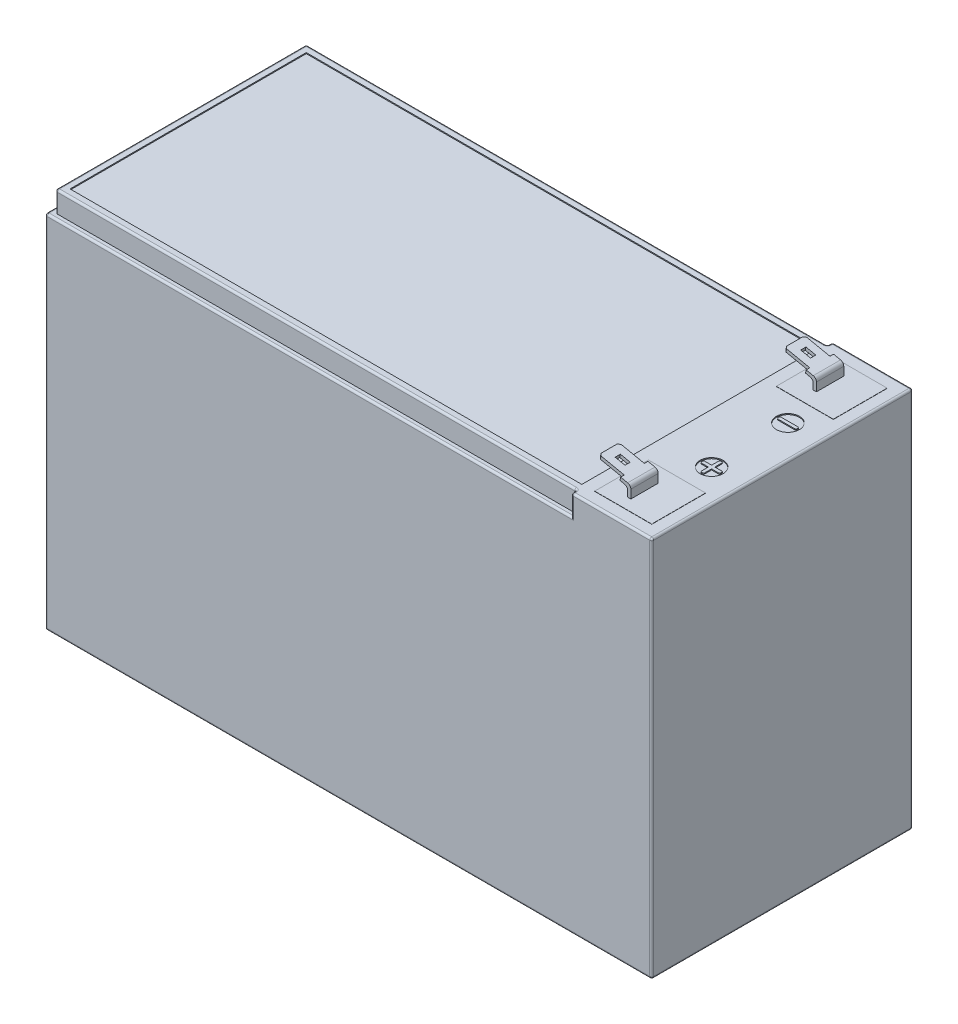
SolidWorks part; units mm, degrees
ref_plane "Front Plane" through (0, 0, 0) normal (0, 0, 1) x (1, 0, 0)
ref_plane "Top Plane" through (0, 0, 0) normal (0, 1, 0) x (1, 0, 0)
ref_plane "Right Plane" through (0, 0, 0) normal (1, 0, 0) x (0, 0, -1)
sketch "Sketch1" plane through (0, 0, 0) normal (0, 1, 0) x (1, 0, 0)
  line L1 (-75.0564, 43.5611) -> (75.9436, 43.5611)
  line L2 (-75.0564, 43.5611) -> (-75.0564, -21.4389)
  line L3 (-75.0564, -21.4389) -> (75.9436, -21.4389)
  line L4 (75.9436, 43.5611) -> (75.9436, -21.4389)
  dimension "D1" = 151
  dimension "D2" = 65
extrude "Boss-Extrude1" add sketch "Sketch1" along normal blind 95
ref_plane "Plane1" through (0, 0, 15.4389) normal (0, 0, 1) x (1, 0, 0)
sketch "Sketch2" plane through (0, 0, 15.4389) normal (0, 0, 1) x (1, 0, 0)
  line L0 (63.9436, 95) -> (63.9436, 97.3257)
  line L1 (-75.0564, 95) -> (75.9436, 95) construction
  line L2 (63.9436, 97.3257) -> (55.7698, 99.03)
  line L3 (55.7698, 99.03) -> (55.9331, 99.8131)
  line L4 (55.9331, 99.8131) -> (64.7436, 97.9761)
  line L5 (64.7436, 97.9761) -> (64.7436, 95)
  line L6 (64.7436, 95) -> (63.9436, 95)
  line L7 (75.9436, 95) -> (75.9436, 0) construction
  dimension "D1" = 12
  dimension "D2" = 9
  dimension "D3" = 0.8
  dimension "D4" = 0.8
extrude "Boss-Extrude2" add sketch "Sketch2" against normal blind 6.8
ref_plane "Plane2" through (0, 0, -11.0611) normal (0, 0, 1) x (1, 0, 0)
sketch "Sketch4" plane through (22.274, 106.8309, 0) normal (0.2041, 0.9789, 0) x (0.9789, -0.2041, 0)
  line L0 (40.7829, -8.6389) -> (40.7829, -9.5389)
  line L1 (43.3829, -8.6389) -> (34.3829, -8.6389) construction
  line L2 (40.7829, -9.5389) -> (34.3829, -9.5389)
  line L3 (34.3829, -8.6389) -> (34.3829, -15.4389) construction
  line L4 (34.3829, -9.5389) -> (34.3829, -8.6389)
  line L5 (34.3829, -8.6389) -> (40.7829, -8.6389)
  line L6 (40.7829, -14.5389) -> (40.7829, -15.4389)
  line L7 (-52.25, -15.4389) -> (52.25, -15.4389) construction
  line L8 (40.7829, -14.5389) -> (34.3829, -14.5389)
  line L9 (34.3829, -14.5389) -> (34.3829, -15.4389)
  line L10 (34.3829, -15.4389) -> (40.7829, -15.4389)
  line L12 (36.5829, -11.3889) -> (39.0829, -11.3889)
  line L13 (36.5829, -11.3889) -> (36.5829, -12.6889)
  line L14 (36.5829, -12.6889) -> (39.0829, -12.6889)
  line L15 (39.0829, -11.3889) -> (39.0829, -12.6889)
  dimension "D1" = 0.9
  dimension "D2" = 0.9
  dimension "D3" = 6.4
  dimension "D4" = 2.2
  dimension "D5" = 2.5
  dimension "D6" = 1.3
  dimension "D7" = 1.85
  dimension "D8" = 1.85
extrude "Cut-Extrude1" cut sketch "Sketch4" against normal up to next (0.8 mm away)
chamfer "Chamfer1" distance 0.5 angle 45 2 edges at (55.8514, 99.4215, 9.5389) (55.8514, 99.4215, 14.5389)
fillet "Fillet1" radius 1 2 edges at (63.9436, 97.3257, 12.0389) (64.7436, 97.9761, 12.0389)
mirror "Mirror1" about plane through (0, 0, -11.0611) normal (0, 0, 1) of "Fillet1", "Chamfer1", "Cut-Extrude1", "Boss-Extrude2"
sketch "Sketch5" plane through (0, 95, 0) normal (0, 1, 0) x (1, 0, 0)
  line L0 (55.9436, -21.4389) -> (55.9436, -20.1389)
  line L1 (-75.0564, -21.4389) -> (75.9436, -21.4389) construction
  line L2 (55.9436, -20.1389) -> (-73.7564, -20.1389)
  line L3 (-73.7564, -20.1389) -> (-73.7564, 42.2611)
  line L4 (-73.7564, 42.2611) -> (55.9436, 42.2611)
  line L5 (55.9436, 42.2611) -> (55.9436, 43.5611)
  line L6 (75.9436, 43.5611) -> (-75.0564, 43.5611) construction
  line L7 (55.9436, 43.5611) -> (-75.0564, 43.5611)
  line L8 (-75.0564, 43.5611) -> (-75.0564, -21.4389)
  line L9 (-75.0564, -21.4389) -> (55.9436, -21.4389)
  line L10 (75.9436, -21.4389) -> (75.9436, 43.5611) construction
  dimension "D1" = 1.3
  dimension "D2" = 1.3
  dimension "D3" = 1.3
  dimension "D4" = 20
  dimension "D5" = 20
extrude "Cut-Extrude2" cut sketch "Sketch5" against normal blind 5.2
fillet "Fillet2" radius 0.5 25 edges at (0.4436, 0, -43.5611) (-75.0564, 44.9, -43.5611) (-75.0564, 0, -11.0611) (-75.0564, 44.9, 21.4389) (75.9436, 0, -11.0611) (0.4436, 0, 21.4389) (75.9436, 47.5, -43.5611) (65.9436, 95, -43.5611) (55.9436, 92.4, -43.5611) (55.9436, 92.4, -42.2611) (55.9436, 95, -42.9111) (-9.5564, 89.8, -43.5611) (-8.9064, 95, -42.2611) (-73.7564, 92.4, -42.2611) (-73.7564, 92.4, 20.1389) (-75.0564, 89.8, -11.0611) (55.9436, 92.4, 20.1389) (-9.5564, 89.8, 21.4389) (55.9436, 92.4, 21.4389) (75.9436, 47.5, 21.4389) (75.9436, 95, -11.0611) (65.9436, 95, 21.4389) (55.9436, 95, 20.7889) (-8.9064, 95, 20.1389) (-73.7564, 95, -11.0611)
sketch "Sketch6" plane through (0, 95, 0) normal (0, 1, 0) x (1, 0, 0)
  line L0 (-73.7564, -19.6389) -> (-73.7564, 41.7611) construction
  line L1 (-71.9564, 40.4611) -> (55.4436, 40.4611)
  line L2 (-71.9564, 40.4611) -> (-71.9564, -18.3389)
  line L3 (-71.9564, -18.3389) -> (55.4436, -18.3389)
  line L4 (55.4436, 40.4611) -> (55.4436, -18.3389)
  line L5 (-73.2564, 42.2611) -> (55.4436, 42.2611) construction
  line L6 (55.4436, -20.1389) -> (-73.2564, -20.1389) construction
  line L7 (75.9436, 43.0611) -> (75.9436, -20.9389) construction
  line L8 (56.4436, 43.5611) -> (75.4436, 43.5611) construction
  line L9 (75.4436, -21.4389) -> (56.4436, -21.4389) construction
  line L10 (67.4436, 3.7111) -> (67.4436, 1.9611)
  line L11 (65.6936, 20.9611) -> (69.9936, 20.9611)
  line L12 (65.4436, 20.7111) -> (65.4436, 20.4111)
  line L13 (65.6936, 20.1611) -> (69.9936, 20.1611)
  line L14 (70.2436, 20.7111) -> (70.2436, 20.4111)
  line L15 (67.4436, 1.9611) -> (65.6936, 1.9611)
  line L16 (65.4436, 1.7111) -> (65.4436, 1.4111)
  line L17 (65.6936, 1.1611) -> (67.4436, 1.1611)
  line L18 (67.4436, 1.1611) -> (67.4436, -0.5889)
  line L19 (67.6936, -0.8389) -> (67.9936, -0.8389)
  line L20 (68.2436, -0.5889) -> (68.2436, 1.1611)
  line L21 (68.2436, 1.1611) -> (69.9936, 1.1611)
  line L22 (70.2436, 1.4111) -> (70.2436, 1.7111)
  line L23 (69.9936, 1.9611) -> (68.2436, 1.9611)
  line L24 (68.2436, 1.9611) -> (68.2436, 3.7111)
  line L25 (67.9936, 3.9611) -> (67.6936, 3.9611)
  line L27 (72.7436, 40.3611) -> (58.5436, 40.3611)
  line L28 (72.7436, 40.3611) -> (72.7436, 26.9611)
  line L29 (72.7436, 26.9611) -> (58.5436, 26.9611)
  line L30 (58.5436, 40.3611) -> (58.5436, 26.9611)
  line L31 (72.7436, -18.2389) -> (58.5436, -18.2389)
  line L32 (72.7436, -18.2389) -> (72.7436, -4.8389)
  line L33 (72.7436, -4.8389) -> (58.5436, -4.8389)
  line L34 (58.5436, -18.2389) -> (58.5436, -4.8389)
  circle A0 centre (67.8436, 20.5611) radius 2.875
  circle A1 centre (67.8436, 1.5611) radius 2.875
  arc A2 (69.9936, 20.1611) -> (70.2436, 20.4111) centre (69.9936, 20.4111) ccw
  arc A3 (70.2436, 20.7111) -> (69.9936, 20.9611) centre (69.9936, 20.7111) ccw
  arc A4 (65.6936, 20.1611) -> (65.4436, 20.4111) centre (65.6936, 20.4111) cw
  arc A5 (65.6936, 20.9611) -> (65.4436, 20.7111) centre (65.6936, 20.7111) ccw
  arc A6 (65.6936, 1.1611) -> (65.4436, 1.4111) centre (65.6936, 1.4111) cw
  arc A7 (65.4436, 1.7111) -> (65.6936, 1.9611) centre (65.6936, 1.7111) cw
  arc A8 (67.6936, -0.8389) -> (67.4436, -0.5889) centre (67.6936, -0.5889) cw
  arc A9 (67.9936, -0.8389) -> (68.2436, -0.5889) centre (67.9936, -0.5889) ccw
  arc A10 (69.9936, 1.1611) -> (70.2436, 1.4111) centre (69.9936, 1.4111) ccw
  arc A11 (70.2436, 1.7111) -> (69.9936, 1.9611) centre (69.9936, 1.7111) ccw
  arc A12 (68.2436, 3.7111) -> (67.9936, 3.9611) centre (67.9936, 3.7111) ccw
  arc A13 (67.6936, 3.9611) -> (67.4436, 3.7111) centre (67.6936, 3.7111) ccw
  dimension "D5" = 5.75
  dimension "D8" = 5.75
  dimension "D27" = 0.25
  dimension "D1" = 1.8
  dimension "D2" = 1.8
  dimension "D3" = 1.8
  dimension "D4" = 20.5
  dimension "D6" = 8.1
  dimension "D7" = 23
  dimension "D9" = 8.1
  dimension "D10" = 23
  dimension "D11" = 0.4
  dimension "D12" = 0.4
  dimension "D13" = 2.4
  dimension "D14" = 2.4
  dimension "D15" = 0.4
  dimension "D16" = 0.4
  dimension "D17" = 0.4
  dimension "D18" = 0.4
  dimension "D19" = 0.4
  dimension "D20" = 0.4
  dimension "D21" = 0.4
  dimension "D22" = 0.4
  dimension "D23" = 2.4
  dimension "D24" = 2.4
  dimension "D25" = 2.4
  dimension "D26" = 2.4
  dimension "D28" = 3.2
  dimension "D29" = 3.2
  dimension "D30" = 14.2
  dimension "D31" = 13.4
  dimension "D32" = 3.2
  dimension "D33" = 3.2
  dimension "D34" = 14.2
  dimension "D35" = 13.4
extrude "Cut-Extrude3" cut sketch "Sketch6" against normal blind 0.25
sketch "Sketch7" plane through (0, 94.75, 0) normal (0, 1, 0) x (1, 0, 0)
  line L0 (58.5436, 26.9611) -> (72.7436, 26.9611) construction
  line L1 (72.7436, 26.9611) -> (72.7436, 40.3611) construction
  line L2 (58.5436, 40.3611) -> (58.5436, 26.9611) construction
  line L3 (72.7436, 40.3611) -> (58.5436, 40.3611) construction
  line L4 (58.5436, 26.9611) -> (72.7436, 26.9611)
  line L5 (72.7436, 26.9611) -> (72.7436, 40.3611)
  line L6 (58.5436, 40.3611) -> (58.5436, 26.9611)
  line L7 (72.7436, 40.3611) -> (58.5436, 40.3611)
extrude "Boss-Extrude3" add sketch "Sketch7" along normal blind 0.3
sketch "Sketch8" plane through (0, 94.75, 0) normal (0, 1, 0) x (1, 0, 0)
  line L0 (58.5436, -18.2389) -> (72.7436, -18.2389) construction
  line L1 (72.7436, -18.2389) -> (72.7436, -4.8389) construction
  line L2 (58.5436, -4.8389) -> (58.5436, -18.2389) construction
  line L3 (72.7436, -4.8389) -> (58.5436, -4.8389) construction
  line L4 (58.5436, -18.2389) -> (72.7436, -18.2389)
  line L5 (72.7436, -18.2389) -> (72.7436, -4.8389)
  line L6 (58.5436, -4.8389) -> (58.5436, -18.2389)
  line L7 (72.7436, -4.8389) -> (58.5436, -4.8389)
extrude "Boss-Extrude4" add sketch "Sketch8" along normal blind 0.3
ref_plane "Plane3" through (0.4436, 0, 0) normal (-1, 0, 0) x (0, 0, 1)
sketch "Sketch9" plane through (0, 0, 0) normal (0, -1, 0) x (1, 0, 0)
  line L0 (-70.0564, 8.7389) -> (-70.0564, 15.9389)
  line L1 (-69.5564, 16.4389) -> (-62.3564, 16.4389)
  line L2 (-61.8564, 15.9389) -> (-61.8564, 14.9389)
  line L3 (-62.3564, 14.4389) -> (-68.0564, 14.4389)
  line L4 (-68.0564, 14.4389) -> (-68.0564, 8.7389)
  line L5 (-68.5564, 8.2389) -> (-69.5564, 8.2389)
  line L6 (-74.5564, 21.4389) -> (75.4436, 21.4389) construction
  line L7 (-75.0564, -43.0611) -> (-75.0564, 20.9389) construction
  arc A0 (-68.5564, 8.2389) -> (-68.0564, 8.7389) centre (-68.5564, 8.7389) ccw
  arc A1 (-69.5564, 8.2389) -> (-70.0564, 8.7389) centre (-69.5564, 8.7389) cw
  arc A2 (-62.3564, 14.4389) -> (-61.8564, 14.9389) centre (-62.3564, 14.9389) ccw
  arc A3 (-61.8564, 15.9389) -> (-62.3564, 16.4389) centre (-62.3564, 15.9389) ccw
  arc A4 (-69.5564, 16.4389) -> (-70.0564, 15.9389) centre (-69.5564, 15.9389) ccw
  dimension "D7" = 0.5
  dimension "D1" = 8.2
  dimension "D2" = 8.2
  dimension "D3" = 2
  dimension "D4" = 2
  dimension "D5" = 5
  dimension "D6" = 5
extrude "Boss-Extrude5" add sketch "Sketch9" along normal blind 0.5
mirror "Mirror2" about plane through (0.4436, 0, 0) normal (-1, 0, 0) of "Boss-Extrude5"
mirror "Mirror3" about plane through (0, 0, -11.0611) normal (0, 0, 1) of "Mirror2", "Boss-Extrude5"
